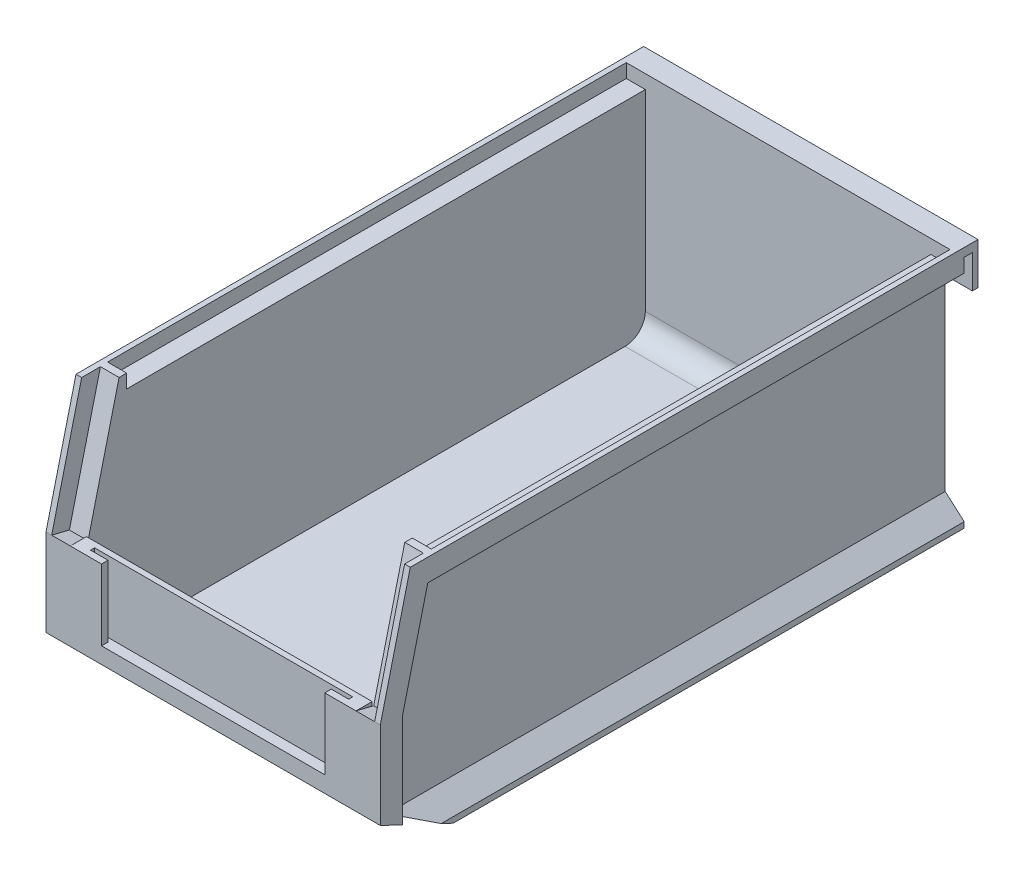
SolidWorks part; units mm, degrees
material "1023 Carbon Steel Sheet (SS)"
ref_plane "Front Plane" through (0, 0, 0) normal (0, 0, 1) x (1, 0, 0)
ref_plane "Top Plane" through (0, 0, 0) normal (0, 1, 0) x (1, 0, 0)
ref_plane "Right Plane" through (0, 0, 0) normal (1, 0, 0) x (0, 0, -1)
sketch "Sketch1" plane through (0, 0, 0) normal (0, 0, 1) x (1, 0, 0)
  line L1 (0, 0) -> (104.775, 0)
  line L2 (0, 0) -> (0, 76.2)
  line L3 (0, 76.2) -> (104.775, 76.2)
  line L4 (104.775, 0) -> (104.775, 76.2)
  dimension "D1" = 104.775
  dimension "D2" = 76.2
extrude "Boss-Extrude1" add sketch "Sketch1" along normal blind 187.325
sketch "Sketch2" plane through (104.775, 0, 0) normal (1, 0, 0) x (0, 0, -1)
  line L0 (0, 0) -> (-4.318, 0)
  line L1 (-187.325, 0) -> (0, 0) construction
  line L2 (-4.318, 0) -> (-4.318, 73.533)
  line L3 (-4.318, 73.533) -> (-1.778, 73.533)
  line L4 (-1.778, 73.533) -> (-1.778, 63.119)
  line L5 (-1.778, 63.119) -> (0, 63.119)
  line L6 (0, 0) -> (0, 76.2) construction
  line L7 (0, 63.119) -> (0, 0)
  line L8 (-187.325, 76.2) -> (0, 76.2) construction
  dimension "D1" = 1.778
  dimension "D2" = 2.667
  dimension "D3" = 4.318
  dimension "D4" = 13.081
extrude "Cut-Extrude1" cut sketch "Sketch2" against normal up to next
sketch "Sketch3" plane through (0, 76.2, 0) normal (0, 1, 0) x (1, 0, 0)
  line L0 (0, -187.325) -> (0, 0) construction
  line L1 (1.651, -169.672) -> (103.124, -169.672)
  line L2 (1.651, -169.672) -> (1.651, -7.112)
  line L3 (1.651, -7.112) -> (103.124, -7.112)
  line L4 (103.124, -169.672) -> (103.124, -7.112)
  line L5 (104.775, -187.325) -> (104.775, 0) construction
  line L6 (104.775, 0) -> (0, 0) construction
  dimension "D1" = 1.651
  dimension "D2" = 1.651
  dimension "D3" = 7.112
  dimension "D4" = 162.56
extrude "Cut-Extrude2" cut sketch "Sketch3" against normal blind 4.318
sketch "Sketch4" plane through (0, 71.882, 0) normal (0, 1, 0) x (1, 0, 0)
  line L0 (104.775, -187.325) -> (104.775, 0) construction
  line L1 (7.62, -7.112) -> (97.155, -7.112)
  line L2 (7.62, -7.112) -> (7.62, -182.245)
  line L3 (7.62, -182.245) -> (97.155, -182.245)
  line L4 (97.155, -7.112) -> (97.155, -182.245)
  line L5 (0, -187.325) -> (0, 0) construction
  line L6 (103.124, -7.112) -> (1.651, -7.112) construction
  line L7 (104.775, -187.325) -> (0, -187.325) construction
  dimension "D1" = 7.62
  dimension "D2" = 7.62
  dimension "D3" = 5.08
extrude "Cut-Extrude3" cut sketch "Sketch4" against normal blind 66.548 and the other way up to next
sketch "Sketch5" plane through (0, 76.2, 0) normal (0, 1, 0) x (1, 0, 0)
  line L0 (1.651, -169.672) -> (7.62, -169.672) construction
  line L1 (7.62, -187.325) -> (97.155, -187.325)
  line L2 (7.62, -187.325) -> (7.62, -172.212)
  line L3 (7.62, -172.212) -> (97.155, -172.212)
  line L4 (97.155, -187.325) -> (97.155, -172.212)
  line L5 (7.62, -7.112) -> (7.62, -182.245) construction
  line L6 (97.155, -169.672) -> (97.155, -182.245) construction
  line L7 (104.775, -187.325) -> (0, -187.325) construction
  dimension "D1" = 2.54
extrude "Cut-Extrude4" cut sketch "Sketch5" against normal blind 38.1
sketch "Sketch6" plane through (0, 0, 0) normal (-1, 0, 0) x (0, 0, 1)
  line L0 (187.325, 38.1) -> (187.325, 76.2)
  line L1 (187.325, 76.2) -> (187.325, 0) construction
  line L2 (187.325, 76.2) -> (177.927, 76.2)
  line L3 (187.325, 76.2) -> (0, 76.2) construction
  line L4 (177.927, 76.2) -> (187.325, 38.1)
  dimension "D1" = 38.1
  dimension "D2" = 9.398
  dimension "D3" = 8.255
extrude "Cut-Extrude5" cut sketch "Sketch6" against normal through all
sketch "Sketch7" plane through (0, 45.7419, 185.44) normal (0, 0.2395, 0.9709) x (1, 0, 0)
  line L0 (0, 31.3711) -> (0, -7.8709) construction
  line L1 (7.62, 35.3091) -> (1.778, 35.3091)
  line L2 (7.62, 35.3091) -> (7.62, -7.8709)
  line L3 (7.62, -7.8709) -> (1.778, -7.8709)
  line L4 (1.778, 35.3091) -> (1.778, -7.8709)
  line L5 (97.155, 35.3091) -> (102.997, 35.3091)
  line L6 (97.155, 35.3091) -> (97.155, -7.8709)
  line L7 (97.155, -7.8709) -> (102.997, -7.8709)
  line L8 (102.997, 35.3091) -> (102.997, -7.8709)
  line L9 (104.775, 31.3711) -> (104.775, -7.8709) construction
  line L10 (7.62, -7.8709) -> (0, -7.8709) construction
  line L11 (104.775, -7.8709) -> (97.155, -7.8709) construction
  dimension "D1" = 1.778
  dimension "D2" = 1.778
  dimension "D3" = 43.18
extrude "Cut-Extrude6" cut sketch "Sketch7" against normal blind 5.715
sketch "Sketch8" plane through (0, 38.1, 0) normal (0, 1, 0) x (1, 0, 0)
  line L0 (92.837, -184.023) -> (11.938, -184.023)
  line L1 (11.938, -184.023) -> (11.938, -185.293)
  line L2 (11.938, -185.293) -> (17.399, -185.293)
  line L3 (17.399, -185.293) -> (17.399, -187.325)
  line L4 (7.62, -187.325) -> (97.155, -187.325) construction
  line L5 (17.399, -187.325) -> (87.376, -187.325)
  line L6 (87.376, -187.325) -> (87.376, -185.293)
  line L7 (87.376, -185.293) -> (92.837, -185.293)
  line L8 (92.837, -185.293) -> (92.837, -184.023)
  line L9 (97.155, -182.245) -> (7.62, -182.245) construction
  dimension "D1" = 1.27
  dimension "D2" = 1.778
  dimension "D3" = 10.16
  dimension "D4" = 10.16
  dimension "D5" = 5.461
  dimension "D6" = 5.461
extrude "Cut-Extrude7" cut sketch "Sketch8" against normal blind 22.225
ref_plane "Plane1" through (52.3875, 0, 0) normal (1, 0, 0) x (0, 0, -1)
sketch "Sketch9" plane through (52.3875, 0, 0) normal (1, 0, 0) x (0, 0, -1)
  line L0 (-184.7444, 66.8968) -> (-192.6816, 58.196) construction
  line L1 (-7.112, 5.334) -> (-182.245, 5.334) construction
  line L2 (-156.845, 5.334) -> (-182.245, 5.334)
  line L3 (-182.245, 36.8469) -> (-182.245, 5.334) construction
  line L4 (-182.245, 27.4489) -> (-182.245, 5.334)
  line L6 (-182.245, 27.4489) -> (-156.845, 5.334)
  dimension "D1" = 25.4
extrude "Boss-Extrude2" add sketch "Sketch9" along normal up to surface and the other way up to surface up to face at (97.155, 47.2814, 144.1444) other way up to face at (7.62, 47.8212, 123.8244)
sketch "Sketch10" plane through (104.775, 0, 0) normal (1, 0, 0) x (0, 0, -1)
  line L0 (-187.325, 10.795) -> (-187.325, 0)
  line L1 (-187.325, 0) -> (-187.325, 38.1) construction
  line L2 (-187.325, 0) -> (-164.465, 0)
  line L3 (-187.325, 0) -> (-4.318, 0) construction
  line L4 (-164.465, 0) -> (-187.325, 10.795)
  dimension "D1" = 22.86
  dimension "D2" = 10.795
extrude "Cut-Extrude8" cut sketch "Sketch10" against normal up to surface (104.775 mm away) up to face at (0, 51.5338, 62.7521)
sketch "Sketch11" plane through (0, 0, 0) normal (-1, 0, 0) x (0, 0, 1)
  line L2 (110.6118, 69.215) -> (4.318, 69.215)
  line L5 (4.318, 6.985) -> (4.318, 69.215)
  line L6 (4.318, 0) -> (4.318, 73.533) construction
  line L7 (88.3868, 69.215) -> (88.3868, 6.985) construction
  line L10 (180.34, 6.985) -> (4.318, 6.985)
  line L12 (180.34, 37.2512) -> (180.34, 6.985)
  line L13 (172.4556, 69.215) -> (180.34, 37.2512)
  line L14 (172.4556, 69.215) -> (110.6118, 69.215)
extrude "Cut-Extrude9" cut sketch "Sketch11" against normal blind 5.969
mirror "Mirror1" about plane through (52.3875, 0, 0) normal (1, 0, 0) of "Cut-Extrude9"
sketch "Sketch12" plane through (0, 0, 0) normal (0, -1, 0) x (1, 0, 0)
  line L0 (0, 164.465) -> (0, 4.318) construction
  line L1 (8.89, 4.318) -> (95.885, 4.318)
  line L2 (8.89, 4.318) -> (8.89, 169.3073)
  line L3 (8.89, 169.3073) -> (95.885, 169.3073)
  line L4 (95.885, 4.318) -> (95.885, 169.3073)
  line L5 (104.775, 164.465) -> (104.775, 4.318) construction
  line L6 (0, 4.318) -> (104.775, 4.318) construction
  dimension "D1" = 8.89
  dimension "D2" = 8.89
extrude "Cut-Extrude10" cut sketch "Sketch12" against normal blind 2.921
sketch "Sketch13" plane through (0, 0, 4.318) normal (0, 0, -1) x (-1, 0, 0)
  line L0 (-5.969, 6.985) -> (0, 6.985)
  line L1 (0, 6.985) -> (0, 1.778)
  line L2 (0, 0) -> (0, 6.985) construction
  line L3 (0, 1.778) -> (-5.969, 6.985)
  line L4 (-98.806, 6.985) -> (-104.775, 6.985)
  line L5 (-104.775, 6.985) -> (-104.775, 1.778)
  line L6 (-104.775, 6.985) -> (-104.775, 0) construction
  line L7 (-104.775, 1.778) -> (-98.806, 6.985)
  line L8 (-95.885, 0) -> (-104.775, 0) construction
  dimension "D1" = 1.778
  dimension "D2" = 1.778
extrude "Cut-Extrude11" cut sketch "Sketch13" against normal through all
fillet "Fillet1" radius 6.35 2 edges at (52.3875, 5.334, 156.845) (52.3875, 5.334, 7.112)
